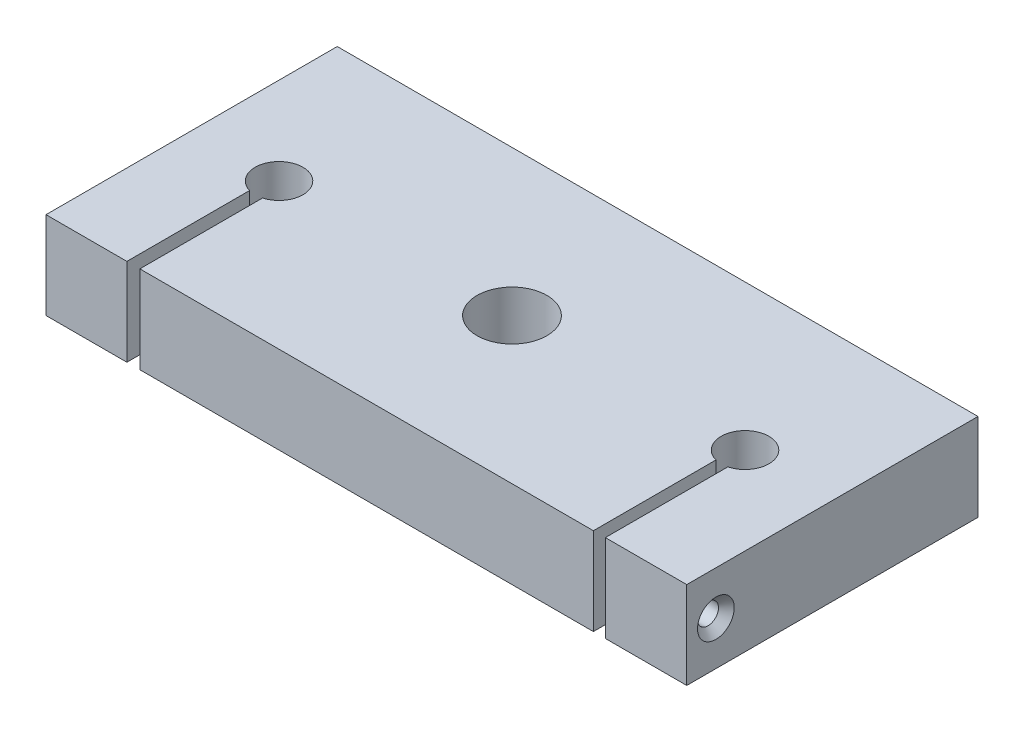
SolidWorks part; units mm, degrees
ref_plane "Front Plane" through (0, 0, 0) normal (0, 0, 1) x (1, 0, 0)
ref_plane "Top Plane" through (0, 0, 0) normal (0, 1, 0) x (1, 0, 0)
ref_plane "Right Plane" through (0, 0, 0) normal (1, 0, 0) x (0, 0, -1)
sketch "Sketch1" plane through (0, 0, 0) normal (0, 1, 0) x (1, 0, 0)
  line L1 (55, -25) -> (-55, -25)
  line L2 (55, -25) -> (55, 25)
  line L3 (55, 25) -> (-55, 25)
  line L4 (-55, -25) -> (-55, 25)
  line L5 (55, -25) -> (-55, 25) construction
  line L6 (55, 25) -> (-55, -25) construction
  circle A0 centre (0, 0) radius 6
  point P0 (0, 0)
  dimension "D3" = 12
  dimension "D1" = 50
  dimension "D2" = 110
extrude "Boss-Extrude2" add sketch "Sketch1" along normal blind 15
sketch "Sketch2" plane through (0, 15, 0) normal (0, 1, 0) x (1, 0, 0)
  line L0 (-41.114, -25) -> (-38.886, -25)
  line L1 (-55, -25) -> (55, -25) construction
  line L2 (38.975, -25) -> (41.025, -25)
  line L3 (-41.114, -3.9389) -> (-41.114, -25)
  line L4 (-38.886, -3.9389) -> (-38.886, -25)
  line L5 (38.975, -3.9629) -> (38.975, -25)
  line L6 (41.025, -3.9629) -> (41.025, -25)
  arc A0 (41.025, -3.9629) -> (38.975, -3.9629) centre (40, 0.0069) ccw
  arc A1 (-38.886, -3.9389) -> (-41.114, -3.9389) centre (-40, 0.0069) ccw
  dimension "D1" = 8.2
  dimension "D2" = 4.1
extrude "Cut-Extrude1" cut sketch "Sketch2" against normal blind 24
hole_wizard "CSK for M3 Flat Head Machine Screw1" positions "Sketch3" profile "Sketch5" countersink size "M3" standard "ANSI Metric"
sketch "Sketch3" plane through (-55, 0, 0) normal (-1, 0, 0) x (0, 0, 1)
  line L0 (-25, 15) -> (25, 15) construction
  line L1 (25, 15) -> (25, 0) construction
  point P0 (20, 7.5)
  dimension "D1" = 7.5
  dimension "D2" = 5
sketch "Sketch5" plane through (-55, 7.5, 20) normal (0, 1, 0) x (0, 0, 1)
  line L0 (0, 0) -> (0, 14.9676)
  line L1 (0, 14.9676) -> (1.8, 13.886)
  line L2 (1.8, 13.886) -> (1.8, 1.35)
  line L3 (1.8, 1.35) -> (3.15, 0)
  line L5 (3.15, 0) -> (0, 0)
  line L6 (-1.8, 1.35) -> (-3.15, 0) construction
  line L10 (0, 14.9676) -> (-1.8, 13.886) construction
  line L11 (0, -6.35) -> (0, 107.95) construction
  dimension "Hole Dia." = 3.6
  dimension "Hole Depth" = 13.886
  dimension "Near C'Sink Dia." = 6.3
  dimension "Near C'Sink Angle" = 90
  dimension "Drill Angle" = 118
hole_wizard "CSK for M3 Flat Head Machine Screw2" positions "Sketch6" profile "Sketch7" countersink size "M3" standard "ANSI Metric"
sketch "Sketch6" plane through (55, 0, 0) normal (1, 0, 0) x (0, 0, -1)
  line L0 (-25, 15) -> (25, 15) construction
  line L1 (-25, 15) -> (-25, 0) construction
  point P0 (-20, 7.5)
  dimension "D1" = 7.5
  dimension "D2" = 5
sketch "Sketch7" plane through (55, 7.5, 20) normal (0, 1, 0) x (0, 0, -1)
  line L0 (0, 0) -> (0, 15.0565)
  line L1 (0, 15.0565) -> (1.8, 13.975)
  line L2 (1.8, 13.975) -> (1.8, 1.35)
  line L3 (1.8, 1.35) -> (3.15, 0)
  line L5 (3.15, 0) -> (0, 0)
  line L6 (-1.8, 1.35) -> (-3.15, 0) construction
  line L10 (0, 15.0565) -> (-1.8, 13.975) construction
  line L11 (0, -6.35) -> (0, 107.95) construction
  dimension "Hole Dia." = 3.6
  dimension "Hole Depth" = 13.975
  dimension "Near C'Sink Dia." = 6.3
  dimension "Near C'Sink Angle" = 90
  dimension "Drill Angle" = 118
hole_wizard "Tap Drill for M3x0.5 Tap1" positions "Sketch10" profile "Sketch11" hole size "M3x0.5" standard "ANSI Metric" end condition through all
sketch "Sketch10" plane through (-38.886, 0, 0) normal (-1, 0, 0) x (0, 0, 1)
  point P0 (20, 7.5)
sketch "Sketch11" plane through (-38.886, 7.5, 20) normal (0, 1, 0) x (0, 0, 1)
  line L0 (0, 0) -> (0, 93.886)
  line L1 (0, 93.886) -> (1.25, 93.886)
  line L2 (1.25, 93.886) -> (1.25, 0)
  line L5 (1.25, 0) -> (0, 0)
  line L11 (0, -6.35) -> (0, 107.95) construction
  dimension "Thru Hole Dia." = 2.5
  dimension "Thru Hole Depth" = 93.886
